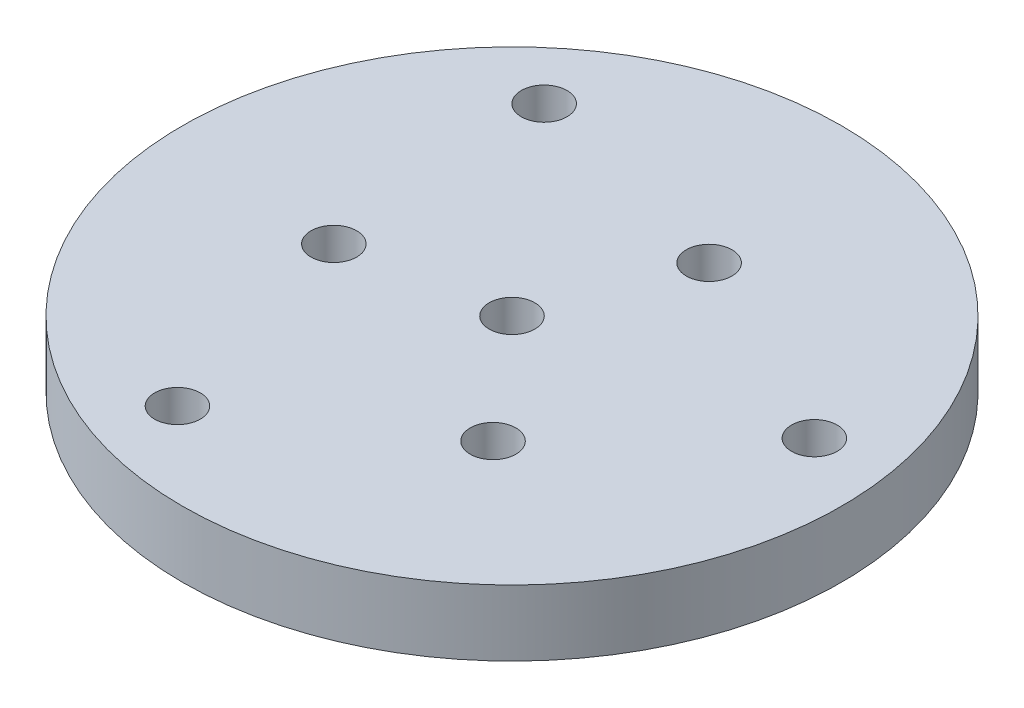
SolidWorks part; units mm, degrees
material "6061-T6 (SS)"
ref_plane "Front Plane" through (0, 0, 0) normal (0, 0, 1) x (1, 0, 0)
ref_plane "Top Plane" through (0, 0, 0) normal (0, 1, 0) x (1, 0, 0)
ref_plane "Right Plane" through (0, 0, 0) normal (1, 0, 0) x (0, 0, -1)
sketch "Sketch1" plane through (0, 0, 0) normal (0, 1, 0) x (1, 0, 0)
  circle A0 centre (0, 0) radius 47.625
  circle A1 centre (0, 0) radius 3.3
  circle A2 centre (0, 25.4) radius 1.5875 construction
  dimension "D1" = 95.25
  dimension "D2" = 6.6
  dimension "D3" = 3.175
  dimension "D4" = 25.4
extrude "Boss-Extrude1" add sketch "Sketch1" along normal mid plane 9.525
ref_plane "Plane1" through (0, 0, 50.8) normal (0, 0, 1) x (1, 0, 0)
sketch "Sketch2" plane through (0, 0, 50.8) normal (0, 0, 1) x (1, 0, 0)
  circle A0 centre (0, 0) radius 1.3526
  dimension "D1" = 2.7051
extrude "Cut-Extrude1" [suppressed] cut sketch "Sketch2" against normal blind 12.7
sketch "Sketch3" plane through (0, 0, 0) normal (0, 0, 1) x (1, 0, 0)
  line L0 (0, 4.7625) -> (0, -4.7625)
  line L1 (47.625, 4.7625) -> (-47.625, 4.7625) construction
  line L2 (-47.625, -4.7625) -> (47.625, -4.7625) construction
pattern_circular "CirPattern1" [suppressed] count 4 over 360 about axis through (0, 4.7625, 0) along (0, -1, 0)
sketch "Sketch4" plane through (0, 4.7625, 0) normal (0, 1, 0) x (1, 0, 0)
  line L0 (0, 0) -> (0, -35.975) construction
  line L1 (-12.9007, -35.4443) -> (0, 0) construction
  line L2 (0, 0) -> (14.286, -17.0253) construction
  circle A0 centre (-12.9007, -35.4443) radius 3.3
  circle A1 centre (-24.2453, 28.8944) radius 3.3
  circle A2 centre (37.146, 6.5498) radius 3.3
  circle A3 centre (14.286, -17.0253) radius 3.3
  circle A4 centre (-21.8874, -3.8593) radius 3.3
  circle A5 centre (7.6014, 20.8847) radius 3.3
  point P12 (0, 0)
  point P19 (0, 0)
  dimension "D1" = 6.6
  dimension "D7" = 6.6
  dimension "D2" = 37.719
  dimension "D3" = 20
  dimension "D5" = 60
  dimension "D6" = 22.225
  dimension "D4" = 3
  dimension "D8" = 3
extrude "Cut-Extrude2" cut sketch "Sketch4" against normal through all
equation "\"Body_Tube_OD\"= 4.024in"
equation "\"Body_Tube_ID\"= 3.90in"
equation "\"SS_Fwd_Bulkhead_OD\"=3.75"
equation "\"D1@Sketch1\"=\"SS_Fwd_Bulkhead_OD\""
equation "\"Bodytube_OD\" = 6.17in"
equation "\"Bodytube_ID\" = 5.998in"
equation "\"Motor_OD\" = 4in"
equation "\"Fwd_Tube_Length\" = 40in"
equation "\"Mid_Tube_Length\" = 1in"
equation "\"Mid_Coupler_Length\" = 13in"
equation "\"Aft_Section_Length\"= 39in"
equation "\"AB_Coupler_OD_Length\"= 1in"
equation "\"AB_Coupling_Section_Length\"= 0.375in"
equation "\"AB_Coupler_Length\"= \"AB_Coupler_OD_Length\" + \"AB_Coupling_Section_Length\" * 2"
equation "\"Cutout_Angle\" = 80"
equation "\"AB_Paddle_Height\" = 0.375in"
equation "\"AB_Coupler_Num_Screws\"= 6"
equation "\"AB_BKHD_Thickness\" = 0.375in"
equation "\"AB_Mount_From_Bottom\" = 23.175in"
equation "\"Num_Cutouts\" = 3"
equation "\"AB_Coupler_OD\"= 6.17in"
equation "\"AB_Coupler_ID\"= 5.75in"
equation "\"AB_Coupler_Surface_Diameter\"= 5.998in"
equation "\"AB_Coupling_Screw_Diameter\"= 0.1065in"
equation "\"AB_Central_Bushing_Length\" = .75in"
equation "\"Lead_Screw_Dist\" = 3.4in"
equation "\"Lead_Screw_Diam\" = 0.386in"
equation "\"Lead_Screw_Length\" = (\"Mid_Coupler_Length\" + 2*0.375in + 2*0.5in)"
equation "\"Paddle_Pin_Offset\" = .25in"
equation "\"Paddle_Pin_Radius\" = 2.25in"
equation "\"SS_Paddle_Pin_Radius\" = 2.25*0.66in"
equation "\"Paddle_Gear_OD\" = 3.2in"
equation "\"Drive_Gear_OD\" = 1.7in"
equation "\"Fwd_BKHD_From_Top\" = 18in"
equation "\"Fin_Thickness\"= .118in"
equation "\"Guiderail_Cutout_Diameter\"= 1.5in"
equation "\"DB9_Hole_Dist\" = 25mm"
equation "\"DB9_Relief_Width\" = 0.47in"
equation "\"DB9_Relief_Hole_Offset\" = 0.09in"
equation "\"Airbrakes_Wire_Hole_Dia\" = .25in"
equation "\"Airbrakes_Wire_Hole_Dist\" = 1.1in"
equation "\"Servo_Gear_Offset\" = 0.5in"
